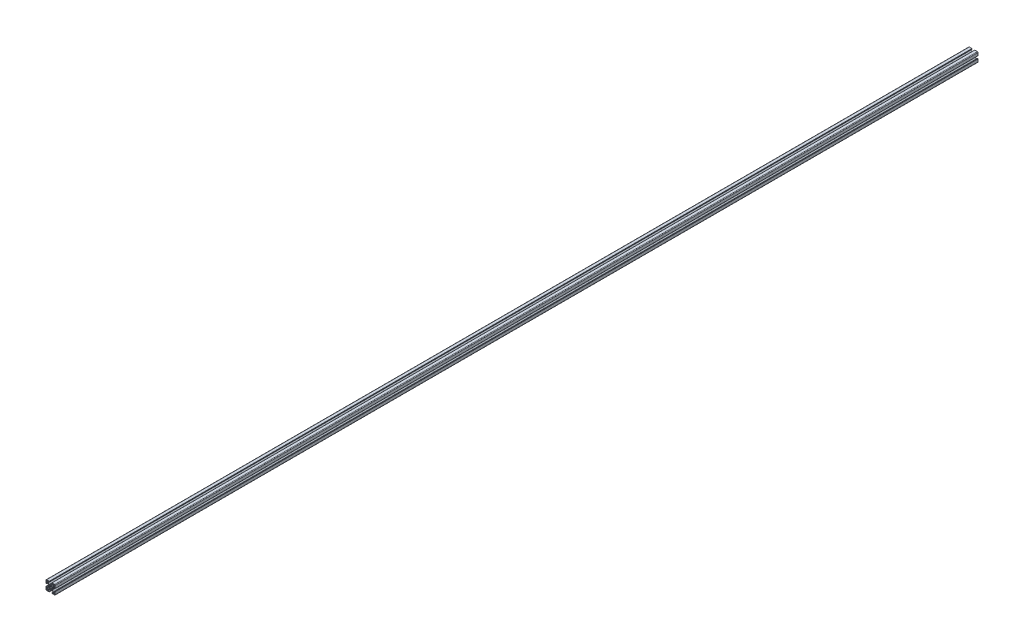
SolidWorks part; units mm, degrees
material "6105-T5 Aluminum"
ref_plane "Front Plane" through (0, 0, 0) normal (0, 0, 1) x (1, 0, 0)
ref_plane "Top Plane" through (0, 0, 0) normal (0, 1, 0) x (1, 0, 0)
ref_plane "Right Plane" through (0, 0, 0) normal (1, 0, 0) x (0, 0, -1)
sketch "Sketch1" plane through (0, 0, 0) normal (0, 0, 1) x (1, 0, 0)
  line L0 (9.5, -13.3189) -> (9.5, -9.88)
  line L1 (9.88, -9.5) -> (13.3189, -9.5)
  line L2 (13.6999, -9.881) -> (13.6999, -12.6999)
  line L3 (12.6999, -13.6999) -> (9.881, -13.6999)
  line L4 (-13.3189, -9.5) -> (-9.88, -9.5)
  line L5 (-9.5, -9.88) -> (-9.5, -13.3189)
  line L6 (-9.881, -13.6999) -> (-12.6999, -13.6999)
  line L7 (-13.6999, -12.6999) -> (-13.6999, -9.881)
  line L8 (-1.4942, -3.1981) -> (-2.4733, -3.9799)
  line L9 (-3.9799, -2.4733) -> (-3.1981, -1.4942)
  line L10 (-3.1981, 1.4942) -> (-3.9799, 2.4733)
  line L11 (-2.4733, 3.9799) -> (-1.4942, 3.1981)
  line L12 (1.4942, 3.1981) -> (2.4733, 3.9799)
  line L13 (3.9799, 2.4733) -> (3.1981, 1.4942)
  line L14 (3.1981, -1.4942) -> (3.9799, -2.4733)
  line L15 (2.4733, -3.9799) -> (1.4942, -3.1981)
  line L16 (-9.5, 13.3189) -> (-9.5, 9.88)
  line L17 (-9.88, 9.5) -> (-13.3189, 9.5)
  line L18 (-13.6999, 9.881) -> (-13.6999, 12.6999)
  line L19 (-12.6999, 13.6999) -> (-9.881, 13.6999)
  line L20 (9.881, 13.6999) -> (12.6999, 13.6999)
  line L21 (13.6999, 12.6999) -> (13.6999, 9.881)
  line L22 (13.3189, 9.5) -> (9.88, 9.5)
  line L23 (9.5, 9.88) -> (9.5, 13.3189)
  line L24 (12.7425, -4.5) -> (12.7425, -7.7325)
  line L25 (12.2428, -8.25) -> (10.2602, -8.25)
  line L26 (9.9066, -8.1035) -> (5.9811, -4.178)
  line L27 (5.8347, -3.8245) -> (5.8347, -1.0125)
  line L28 (5.8347, -1.0125) -> (5.3247, -0.0625)
  line L29 (5.3247, -0.0625) -> (5.8347, 0.8875)
  line L30 (5.8347, 0.8875) -> (5.8347, 3.8245)
  line L31 (5.9811, 4.178) -> (9.9066, 8.1035)
  line L32 (10.2602, 8.25) -> (12.2428, 8.25)
  line L33 (12.7425, 7.7325) -> (12.7425, 4.5)
  line L34 (13.2425, 4) -> (14.4999, 4)
  line L35 (14.9999, 4.5) -> (14.9999, 12.9999)
  line L36 (12.9999, 14.9999) -> (4.5, 14.9999)
  line L37 (4, 14.4999) -> (4, 13.2425)
  line L38 (4.5, 12.7425) -> (7.7325, 12.7425)
  line L39 (8.25, 12.2428) -> (8.25, 10.2602)
  line L40 (8.1035, 9.9066) -> (4.178, 5.9811)
  line L41 (3.8245, 5.8347) -> (0.95, 5.8347)
  line L42 (0.95, 5.8347) -> (0, 5.3247)
  line L43 (0, 5.3247) -> (-0.95, 5.8347)
  line L44 (-0.95, 5.8347) -> (-3.8245, 5.8347)
  line L45 (-4.178, 5.9811) -> (-8.1035, 9.9066)
  line L46 (-8.25, 10.2602) -> (-8.25, 12.2428)
  line L47 (-7.7325, 12.7425) -> (-4.5, 12.7425)
  line L48 (-4, 13.2425) -> (-4, 14.4999)
  line L49 (-4.5, 14.9999) -> (-12.9999, 14.9999)
  line L50 (-14.9999, 12.9999) -> (-14.9999, 4.5)
  line L51 (-14.4999, 4) -> (-13.2425, 4)
  line L52 (-12.7425, 4.5) -> (-12.7425, 7.7325)
  line L53 (-12.2428, 8.25) -> (-10.2602, 8.25)
  line L54 (-9.9066, 8.1035) -> (-5.9811, 4.178)
  line L55 (-5.8347, 3.8245) -> (-5.8347, 0.8875)
  line L56 (-5.8347, 0.8875) -> (-5.3247, -0.0625)
  line L57 (-5.3247, -0.0625) -> (-5.8347, -1.0125)
  line L58 (-5.8347, -1.0125) -> (-5.8347, -3.8245)
  line L59 (-5.9811, -4.178) -> (-9.9066, -8.1035)
  line L60 (-10.2602, -8.25) -> (-12.2428, -8.25)
  line L61 (-12.7425, -7.7325) -> (-12.7425, -4.5)
  line L62 (-13.2425, -4) -> (-14.4999, -4)
  line L63 (-14.9999, -4.5) -> (-14.9999, -12.9999)
  line L64 (-12.9999, -14.9999) -> (-4.5, -14.9999)
  line L65 (-4, -14.4999) -> (-4, -13.2425)
  line L66 (-4.5, -12.7425) -> (-7.7325, -12.7425)
  line L67 (-8.25, -12.2428) -> (-8.25, -10.2602)
  line L68 (-8.1035, -9.9066) -> (-4.178, -5.9811)
  line L69 (-3.8245, -5.8347) -> (-0.95, -5.8347)
  line L70 (-0.95, -5.8347) -> (0, -5.3247)
  line L71 (0, -5.3247) -> (0.95, -5.8347)
  line L72 (0.95, -5.8347) -> (3.8245, -5.8347)
  line L73 (4.178, -5.9811) -> (8.1035, -9.9066)
  line L74 (8.25, -10.2602) -> (8.25, -12.2428)
  line L75 (7.7325, -12.7425) -> (4.5, -12.7425)
  line L76 (4, -13.2425) -> (4, -14.4999)
  line L77 (4.5, -14.9999) -> (12.9999, -14.9999)
  line L78 (14.9999, -12.9999) -> (14.9999, -4.5)
  line L79 (14.4999, -4) -> (13.2425, -4)
  arc A0 (9.5, -13.3189) -> (9.881, -13.6999) centre (9.881, -13.3189) ccw
  arc A1 (9.88, -9.5) -> (9.5, -9.88) centre (9.88, -9.88) ccw
  arc A2 (13.6999, -9.881) -> (13.3189, -9.5) centre (13.3189, -9.881) ccw
  arc A3 (12.6999, -13.6999) -> (13.6999, -12.6999) centre (12.6999, -12.6999) ccw
  arc A4 (-13.3189, -9.5) -> (-13.6999, -9.881) centre (-13.3189, -9.881) ccw
  arc A5 (-9.5, -9.88) -> (-9.88, -9.5) centre (-9.88, -9.88) ccw
  arc A6 (-9.881, -13.6999) -> (-9.5, -13.3189) centre (-9.881, -13.3189) ccw
  arc A7 (-13.6999, -12.6999) -> (-12.6999, -13.6999) centre (-12.6999, -12.6999) ccw
  arc A8 (-1.4942, -3.1981) -> (1.4942, -3.1981) centre (0, 0) ccw
  arc A9 (-3.9799, -2.4733) -> (-2.4733, -3.9799) centre (-3.1422, -3.1422) ccw
  arc A10 (-3.1981, 1.4942) -> (-3.1981, -1.4942) centre (0, 0) ccw
  arc A11 (-2.4733, 3.9799) -> (-3.9799, 2.4733) centre (-3.1422, 3.1422) ccw
  arc A12 (1.4942, 3.1981) -> (-1.4942, 3.1981) centre (0, 0) ccw
  arc A13 (3.9799, 2.4733) -> (2.4733, 3.9799) centre (3.1422, 3.1422) ccw
  arc A14 (3.1981, -1.4942) -> (3.1981, 1.4942) centre (0, 0) ccw
  arc A15 (2.4733, -3.9799) -> (3.9799, -2.4733) centre (3.1422, -3.1422) ccw
  arc A16 (-9.5, 13.3189) -> (-9.881, 13.6999) centre (-9.881, 13.3189) ccw
  arc A17 (-9.88, 9.5) -> (-9.5, 9.88) centre (-9.88, 9.88) ccw
  arc A18 (-13.6999, 9.881) -> (-13.3189, 9.5) centre (-13.3189, 9.881) ccw
  arc A19 (-12.6999, 13.6999) -> (-13.6999, 12.6999) centre (-12.6999, 12.6999) ccw
  arc A20 (9.881, 13.6999) -> (9.5, 13.3189) centre (9.881, 13.3189) ccw
  arc A21 (13.6999, 12.6999) -> (12.6999, 13.6999) centre (12.6999, 12.6999) ccw
  arc A22 (13.3189, 9.5) -> (13.6999, 9.881) centre (13.3189, 9.881) ccw
  arc A23 (9.5, 9.88) -> (9.88, 9.5) centre (9.88, 9.88) ccw
  arc A24 (13.2425, -4) -> (12.7425, -4.5) centre (13.2425, -4.5) ccw
  arc A25 (12.2428, -8.25) -> (12.7425, -7.7325) centre (12.2428, -7.75) ccw
  arc A26 (9.9066, -8.1035) -> (10.2602, -8.25) centre (10.2602, -7.75) ccw
  arc A27 (5.8347, -3.8245) -> (5.9811, -4.178) centre (6.3347, -3.8245) ccw
  arc A28 (5.9811, 4.178) -> (5.8347, 3.8245) centre (6.3347, 3.8245) ccw
  arc A29 (10.2602, 8.25) -> (9.9066, 8.1035) centre (10.2602, 7.75) ccw
  arc A30 (12.7425, 7.7325) -> (12.2428, 8.25) centre (12.2428, 7.75) ccw
  arc A31 (12.7425, 4.5) -> (13.2425, 4) centre (13.2425, 4.5) ccw
  arc A32 (14.4999, 4) -> (14.9999, 4.5) centre (14.4999, 4.5) ccw
  arc A33 (14.9999, 12.9999) -> (12.9999, 14.9999) centre (12.9999, 12.9999) ccw
  arc A34 (4.5, 14.9999) -> (4, 14.4999) centre (4.5, 14.4999) ccw
  arc A35 (4, 13.2425) -> (4.5, 12.7425) centre (4.5, 13.2425) ccw
  arc A36 (8.25, 12.2428) -> (7.7325, 12.7425) centre (7.75, 12.2428) ccw
  arc A37 (8.1035, 9.9066) -> (8.25, 10.2602) centre (7.75, 10.2602) ccw
  arc A38 (3.8245, 5.8347) -> (4.178, 5.9811) centre (3.8245, 6.3347) ccw
  arc A39 (-4.178, 5.9811) -> (-3.8245, 5.8347) centre (-3.8245, 6.3347) ccw
  arc A40 (-8.25, 10.2602) -> (-8.1035, 9.9066) centre (-7.75, 10.2602) ccw
  arc A41 (-7.7325, 12.7425) -> (-8.25, 12.2428) centre (-7.75, 12.2428) ccw
  arc A42 (-4.5, 12.7425) -> (-4, 13.2425) centre (-4.5, 13.2425) ccw
  arc A43 (-4, 14.4999) -> (-4.5, 14.9999) centre (-4.5, 14.4999) ccw
  arc A44 (-12.9999, 14.9999) -> (-14.9999, 12.9999) centre (-12.9999, 12.9999) ccw
  arc A45 (-14.9999, 4.5) -> (-14.4999, 4) centre (-14.4999, 4.5) ccw
  arc A46 (-13.2425, 4) -> (-12.7425, 4.5) centre (-13.2425, 4.5) ccw
  arc A47 (-12.2428, 8.25) -> (-12.7425, 7.7325) centre (-12.2428, 7.75) ccw
  arc A48 (-9.9066, 8.1035) -> (-10.2602, 8.25) centre (-10.2602, 7.75) ccw
  arc A49 (-5.8347, 3.8245) -> (-5.9811, 4.178) centre (-6.3347, 3.8245) ccw
  arc A50 (-5.9811, -4.178) -> (-5.8347, -3.8245) centre (-6.3347, -3.8245) ccw
  arc A51 (-10.2602, -8.25) -> (-9.9066, -8.1035) centre (-10.2602, -7.75) ccw
  arc A52 (-12.7425, -7.7325) -> (-12.2428, -8.25) centre (-12.2428, -7.75) ccw
  arc A53 (-12.7425, -4.5) -> (-13.2425, -4) centre (-13.2425, -4.5) ccw
  arc A54 (-14.4999, -4) -> (-14.9999, -4.5) centre (-14.4999, -4.5) ccw
  arc A55 (-14.9999, -12.9999) -> (-12.9999, -14.9999) centre (-12.9999, -12.9999) ccw
  arc A56 (-4.5, -14.9999) -> (-4, -14.4999) centre (-4.5, -14.4999) ccw
  arc A57 (-4, -13.2425) -> (-4.5, -12.7425) centre (-4.5, -13.2425) ccw
  arc A58 (-8.25, -12.2428) -> (-7.7325, -12.7425) centre (-7.75, -12.2428) ccw
  arc A59 (-8.1035, -9.9066) -> (-8.25, -10.2602) centre (-7.75, -10.2602) ccw
  arc A60 (-3.8245, -5.8347) -> (-4.178, -5.9811) centre (-3.8245, -6.3347) ccw
  arc A61 (4.178, -5.9811) -> (3.8245, -5.8347) centre (3.8245, -6.3347) ccw
  arc A62 (8.25, -10.2602) -> (8.1035, -9.9066) centre (7.75, -10.2602) ccw
  arc A63 (7.7325, -12.7425) -> (8.25, -12.2428) centre (7.75, -12.2428) ccw
  arc A64 (4.5, -12.7425) -> (4, -13.2425) centre (4.5, -13.2425) ccw
  arc A65 (4, -14.4999) -> (4.5, -14.9999) centre (4.5, -14.4999) ccw
  arc A66 (12.9999, -14.9999) -> (14.9999, -12.9999) centre (12.9999, -12.9999) ccw
  arc A67 (14.9999, -4.5) -> (14.4999, -4) centre (14.4999, -4.5) ccw
extrude "Extrude1" add sketch "Sketch1" against normal blind 3000
